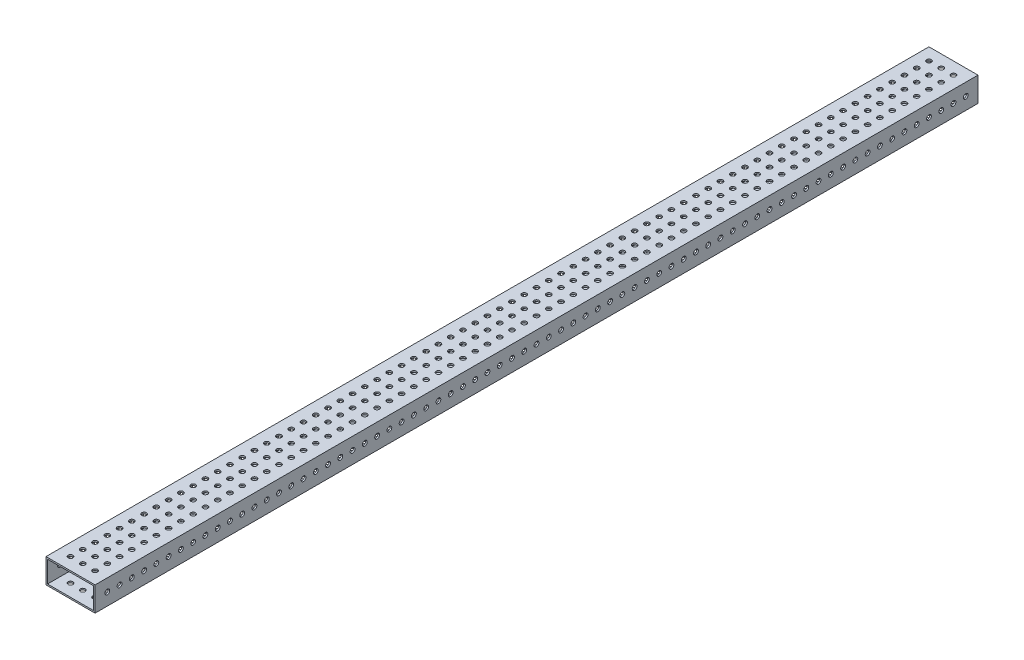
SolidWorks part; units mm, degrees
material "6061 Alloy"
ref_plane "Front Plane" through (0, 0, 0) normal (0, 0, 1) x (1, 0, 0)
ref_plane "Top Plane" through (0, 0, 0) normal (0, 1, 0) x (1, 0, 0)
ref_plane "Right Plane" through (0, 0, 0) normal (1, 0, 0) x (0, 0, -1)
sketch "Sketch1" plane through (0, 0, 0) normal (0, 0, 1) x (1, 0, 0)
  line L0 (1.5875, 1.5875) -> (49.2125, 1.5875)
  line L1 (0, 0) -> (50.8, 0)
  line L2 (0, 0) -> (0, 25.4)
  line L3 (0, 25.4) -> (50.8, 25.4)
  line L4 (50.8, 0) -> (50.8, 25.4)
  line L5 (49.2125, 1.5875) -> (49.2125, 23.8125)
  line L6 (1.5875, 23.8125) -> (49.2125, 23.8125)
  line L7 (1.5875, 1.5875) -> (1.5875, 23.8125)
  dimension "D1" = 50.8
  dimension "D2" = 25.4
  dimension "D3" = 1.5875
extrude "Boss-Extrude1" add sketch "Sketch1" along normal blind 914.4
sketch "Sketch2" plane through (50.8, 0, 0) normal (1, 0, 0) x (0, 0, -1)
  line L0 (-914.4, 0) -> (-914.4, 25.4) construction
  line L1 (-901.7, 12.7) -> (-889, 12.7) construction
  circle A0 centre (-901.7, 12.7) radius 2.4892
  circle A1 centre (-889, 12.7) radius 2.4892
  circle A2 centre (-876.3, 12.7) radius 2.4892
  circle A3 centre (-863.6, 12.7) radius 2.4892
  circle A4 centre (-850.9, 12.7) radius 2.4892
  circle A5 centre (-838.2, 12.7) radius 2.4892
  circle A6 centre (-825.5, 12.7) radius 2.4892
  circle A7 centre (-812.8, 12.7) radius 2.4892
  circle A8 centre (-800.1, 12.7) radius 2.4892
  circle A9 centre (-787.4, 12.7) radius 2.4892
  circle A10 centre (-774.7, 12.7) radius 2.4892
  circle A11 centre (-762, 12.7) radius 2.4892
  circle A12 centre (-749.3, 12.7) radius 2.4892
  circle A13 centre (-736.6, 12.7) radius 2.4892
  circle A14 centre (-723.9, 12.7) radius 2.4892
  circle A15 centre (-711.2, 12.7) radius 2.4892
  circle A16 centre (-698.5, 12.7) radius 2.4892
  circle A17 centre (-685.8, 12.7) radius 2.4892
  circle A18 centre (-673.1, 12.7) radius 2.4892
  circle A19 centre (-660.4, 12.7) radius 2.4892
  circle A20 centre (-647.7, 12.7) radius 2.4892
  circle A21 centre (-635, 12.7) radius 2.4892
  circle A22 centre (-622.3, 12.7) radius 2.4892
  circle A23 centre (-609.6, 12.7) radius 2.4892
  circle A24 centre (-596.9, 12.7) radius 2.4892
  circle A25 centre (-584.2, 12.7) radius 2.4892
  circle A26 centre (-571.5, 12.7) radius 2.4892
  circle A27 centre (-558.8, 12.7) radius 2.4892
  circle A28 centre (-546.1, 12.7) radius 2.4892
  circle A29 centre (-533.4, 12.7) radius 2.4892
  circle A30 centre (-520.7, 12.7) radius 2.4892
  circle A31 centre (-508, 12.7) radius 2.4892
  circle A32 centre (-495.3, 12.7) radius 2.4892
  circle A33 centre (-482.6, 12.7) radius 2.4892
  circle A34 centre (-469.9, 12.7) radius 2.4892
  circle A35 centre (-457.2, 12.7) radius 2.4892
  circle A36 centre (-444.5, 12.7) radius 2.4892
  circle A37 centre (-431.8, 12.7) radius 2.4892
  circle A38 centre (-419.1, 12.7) radius 2.4892
  circle A39 centre (-406.4, 12.7) radius 2.4892
  circle A40 centre (-393.7, 12.7) radius 2.4892
  circle A41 centre (-381, 12.7) radius 2.4892
  circle A42 centre (-368.3, 12.7) radius 2.4892
  circle A43 centre (-355.6, 12.7) radius 2.4892
  circle A44 centre (-342.9, 12.7) radius 2.4892
  circle A45 centre (-330.2, 12.7) radius 2.4892
  circle A46 centre (-317.5, 12.7) radius 2.4892
  circle A47 centre (-304.8, 12.7) radius 2.4892
  circle A48 centre (-292.1, 12.7) radius 2.4892
  circle A49 centre (-279.4, 12.7) radius 2.4892
  circle A50 centre (-266.7, 12.7) radius 2.4892
  circle A51 centre (-254, 12.7) radius 2.4892
  circle A52 centre (-241.3, 12.7) radius 2.4892
  circle A53 centre (-228.6, 12.7) radius 2.4892
  circle A54 centre (-215.9, 12.7) radius 2.4892
  circle A55 centre (-203.2, 12.7) radius 2.4892
  circle A56 centre (-190.5, 12.7) radius 2.4892
  circle A57 centre (-177.8, 12.7) radius 2.4892
  circle A58 centre (-165.1, 12.7) radius 2.4892
  circle A59 centre (-152.4, 12.7) radius 2.4892
  circle A60 centre (-139.7, 12.7) radius 2.4892
  circle A61 centre (-127, 12.7) radius 2.4892
  circle A62 centre (-114.3, 12.7) radius 2.4892
  circle A63 centre (-101.6, 12.7) radius 2.4892
  circle A64 centre (-88.9, 12.7) radius 2.4892
  circle A65 centre (-76.2, 12.7) radius 2.4892
  circle A66 centre (-63.5, 12.7) radius 2.4892
  circle A67 centre (-50.8, 12.7) radius 2.4892
  circle A68 centre (-38.1, 12.7) radius 2.4892
  circle A69 centre (-25.4, 12.7) radius 2.4892
  circle A70 centre (-12.7, 12.7) radius 2.4892
  point P5 (-914.4, 12.7)
  dimension "D1" = 4.9784
  dimension "D3" = 71
  dimension "D2" = 12.7
  dimension "D4" = 12.7
extrude "Cut-Extrude1" cut sketch "Sketch2" against normal through all
sketch "Sketch3" plane through (0, 25.4, 0) normal (0, 1, 0) x (1, 0, 0)
  line L0 (50.8, 0) -> (0, 0) construction
  line L1 (0, -914.4) -> (0, 0) construction
  line L2 (12.7, -12.7) -> (25.4, -12.7) construction
  line L3 (12.7, -12.7) -> (12.7, -25.4) construction
  line L4 (50.8, -914.4) -> (50.8, 0) construction
  circle A0 centre (12.7, -12.7) radius 2.4892
  circle A1 centre (25.4, -12.7) radius 2.4892
  circle A2 centre (38.1, -12.7) radius 2.4892
  circle A3 centre (25.4, -25.4) radius 2.4892
  circle A4 centre (38.1, -25.4) radius 2.4892
  circle A5 centre (25.4, -38.1) radius 2.4892
  circle A6 centre (38.1, -38.1) radius 2.4892
  circle A7 centre (25.4, -50.8) radius 2.4892
  circle A8 centre (38.1, -50.8) radius 2.4892
  circle A9 centre (25.4, -63.5) radius 2.4892
  circle A10 centre (38.1, -63.5) radius 2.4892
  circle A11 centre (25.4, -76.2) radius 2.4892
  circle A12 centre (38.1, -76.2) radius 2.4892
  circle A13 centre (25.4, -88.9) radius 2.4892
  circle A14 centre (38.1, -88.9) radius 2.4892
  circle A15 centre (25.4, -101.6) radius 2.4892
  circle A16 centre (38.1, -101.6) radius 2.4892
  circle A17 centre (25.4, -114.3) radius 2.4892
  circle A18 centre (38.1, -114.3) radius 2.4892
  circle A19 centre (25.4, -127) radius 2.4892
  circle A20 centre (38.1, -127) radius 2.4892
  circle A21 centre (25.4, -139.7) radius 2.4892
  circle A22 centre (38.1, -139.7) radius 2.4892
  circle A23 centre (25.4, -152.4) radius 2.4892
  circle A24 centre (38.1, -152.4) radius 2.4892
  circle A25 centre (25.4, -165.1) radius 2.4892
  circle A26 centre (38.1, -165.1) radius 2.4892
  circle A27 centre (25.4, -177.8) radius 2.4892
  circle A28 centre (38.1, -177.8) radius 2.4892
  circle A29 centre (25.4, -190.5) radius 2.4892
  circle A30 centre (38.1, -190.5) radius 2.4892
  circle A31 centre (25.4, -203.2) radius 2.4892
  circle A32 centre (38.1, -203.2) radius 2.4892
  circle A33 centre (25.4, -215.9) radius 2.4892
  circle A34 centre (38.1, -215.9) radius 2.4892
  circle A35 centre (25.4, -228.6) radius 2.4892
  circle A36 centre (38.1, -228.6) radius 2.4892
  circle A37 centre (25.4, -241.3) radius 2.4892
  circle A38 centre (38.1, -241.3) radius 2.4892
  circle A39 centre (25.4, -254) radius 2.4892
  circle A40 centre (38.1, -254) radius 2.4892
  circle A41 centre (25.4, -266.7) radius 2.4892
  circle A42 centre (38.1, -266.7) radius 2.4892
  circle A43 centre (25.4, -279.4) radius 2.4892
  circle A44 centre (38.1, -279.4) radius 2.4892
  circle A45 centre (25.4, -292.1) radius 2.4892
  circle A46 centre (38.1, -292.1) radius 2.4892
  circle A47 centre (25.4, -304.8) radius 2.4892
  circle A48 centre (38.1, -304.8) radius 2.4892
  circle A49 centre (25.4, -317.5) radius 2.4892
  circle A50 centre (38.1, -317.5) radius 2.4892
  circle A51 centre (25.4, -330.2) radius 2.4892
  circle A52 centre (38.1, -330.2) radius 2.4892
  circle A53 centre (25.4, -342.9) radius 2.4892
  circle A54 centre (38.1, -342.9) radius 2.4892
  circle A55 centre (25.4, -355.6) radius 2.4892
  circle A56 centre (38.1, -355.6) radius 2.4892
  circle A57 centre (25.4, -368.3) radius 2.4892
  circle A58 centre (38.1, -368.3) radius 2.4892
  circle A59 centre (25.4, -381) radius 2.4892
  circle A60 centre (38.1, -381) radius 2.4892
  circle A61 centre (25.4, -393.7) radius 2.4892
  circle A62 centre (38.1, -393.7) radius 2.4892
  circle A63 centre (25.4, -406.4) radius 2.4892
  circle A64 centre (38.1, -406.4) radius 2.4892
  circle A65 centre (25.4, -419.1) radius 2.4892
  circle A66 centre (38.1, -419.1) radius 2.4892
  circle A67 centre (25.4, -431.8) radius 2.4892
  circle A68 centre (38.1, -431.8) radius 2.4892
  circle A69 centre (25.4, -444.5) radius 2.4892
  circle A70 centre (38.1, -444.5) radius 2.4892
  circle A71 centre (25.4, -457.2) radius 2.4892
  circle A72 centre (38.1, -457.2) radius 2.4892
  circle A73 centre (25.4, -469.9) radius 2.4892
  circle A74 centre (38.1, -469.9) radius 2.4892
  circle A75 centre (25.4, -482.6) radius 2.4892
  circle A76 centre (38.1, -482.6) radius 2.4892
  circle A77 centre (25.4, -495.3) radius 2.4892
  circle A78 centre (38.1, -495.3) radius 2.4892
  circle A79 centre (25.4, -508) radius 2.4892
  circle A80 centre (38.1, -508) radius 2.4892
  circle A81 centre (25.4, -520.7) radius 2.4892
  circle A82 centre (38.1, -520.7) radius 2.4892
  circle A83 centre (25.4, -533.4) radius 2.4892
  circle A84 centre (38.1, -533.4) radius 2.4892
  circle A85 centre (25.4, -546.1) radius 2.4892
  circle A86 centre (38.1, -546.1) radius 2.4892
  circle A87 centre (25.4, -558.8) radius 2.4892
  circle A88 centre (38.1, -558.8) radius 2.4892
  circle A89 centre (25.4, -571.5) radius 2.4892
  circle A90 centre (38.1, -571.5) radius 2.4892
  circle A91 centre (25.4, -584.2) radius 2.4892
  circle A92 centre (38.1, -584.2) radius 2.4892
  circle A93 centre (25.4, -596.9) radius 2.4892
  circle A94 centre (38.1, -596.9) radius 2.4892
  circle A95 centre (25.4, -609.6) radius 2.4892
  circle A96 centre (38.1, -609.6) radius 2.4892
  circle A97 centre (25.4, -622.3) radius 2.4892
  circle A98 centre (38.1, -622.3) radius 2.4892
  circle A99 centre (25.4, -635) radius 2.4892
  circle A100 centre (38.1, -635) radius 2.4892
  circle A101 centre (25.4, -647.7) radius 2.4892
  circle A102 centre (38.1, -647.7) radius 2.4892
  circle A103 centre (25.4, -660.4) radius 2.4892
  circle A104 centre (38.1, -660.4) radius 2.4892
  circle A105 centre (25.4, -673.1) radius 2.4892
  circle A106 centre (38.1, -673.1) radius 2.4892
  circle A107 centre (25.4, -685.8) radius 2.4892
  circle A108 centre (38.1, -685.8) radius 2.4892
  circle A109 centre (25.4, -698.5) radius 2.4892
  circle A110 centre (38.1, -698.5) radius 2.4892
  circle A111 centre (25.4, -711.2) radius 2.4892
  circle A112 centre (38.1, -711.2) radius 2.4892
  circle A113 centre (25.4, -723.9) radius 2.4892
  circle A114 centre (38.1, -723.9) radius 2.4892
  circle A115 centre (25.4, -736.6) radius 2.4892
  circle A116 centre (38.1, -736.6) radius 2.4892
  circle A117 centre (25.4, -749.3) radius 2.4892
  circle A118 centre (38.1, -749.3) radius 2.4892
  circle A119 centre (25.4, -762) radius 2.4892
  circle A120 centre (38.1, -762) radius 2.4892
  circle A121 centre (25.4, -774.7) radius 2.4892
  circle A122 centre (38.1, -774.7) radius 2.4892
  circle A123 centre (25.4, -787.4) radius 2.4892
  circle A124 centre (38.1, -787.4) radius 2.4892
  circle A125 centre (25.4, -800.1) radius 2.4892
  circle A126 centre (38.1, -800.1) radius 2.4892
  circle A127 centre (25.4, -812.8) radius 2.4892
  circle A128 centre (38.1, -812.8) radius 2.4892
  circle A129 centre (25.4, -825.5) radius 2.4892
  circle A130 centre (38.1, -825.5) radius 2.4892
  circle A131 centre (25.4, -838.2) radius 2.4892
  circle A132 centre (38.1, -838.2) radius 2.4892
  circle A133 centre (25.4, -850.9) radius 2.4892
  circle A134 centre (38.1, -850.9) radius 2.4892
  circle A135 centre (25.4, -863.6) radius 2.4892
  circle A136 centre (38.1, -863.6) radius 2.4892
  circle A137 centre (25.4, -876.3) radius 2.4892
  circle A138 centre (38.1, -876.3) radius 2.4892
  circle A139 centre (25.4, -889) radius 2.4892
  circle A140 centre (38.1, -889) radius 2.4892
  circle A141 centre (25.4, -901.7) radius 2.4892
  circle A142 centre (38.1, -901.7) radius 2.4892
  circle A145 centre (12.7, -25.4) radius 2.4892
  circle A146 centre (12.7, -38.1) radius 2.4892
  circle A147 centre (12.7, -50.8) radius 2.4892
  circle A148 centre (12.7, -63.5) radius 2.4892
  circle A149 centre (12.7, -76.2) radius 2.4892
  circle A150 centre (12.7, -88.9) radius 2.4892
  circle A151 centre (12.7, -101.6) radius 2.4892
  circle A152 centre (12.7, -114.3) radius 2.4892
  circle A153 centre (12.7, -127) radius 2.4892
  circle A154 centre (12.7, -139.7) radius 2.4892
  circle A155 centre (12.7, -152.4) radius 2.4892
  circle A156 centre (12.7, -165.1) radius 2.4892
  circle A157 centre (12.7, -177.8) radius 2.4892
  circle A158 centre (12.7, -190.5) radius 2.4892
  circle A159 centre (12.7, -203.2) radius 2.4892
  circle A160 centre (12.7, -215.9) radius 2.4892
  circle A161 centre (12.7, -228.6) radius 2.4892
  circle A162 centre (12.7, -241.3) radius 2.4892
  circle A163 centre (12.7, -254) radius 2.4892
  circle A164 centre (12.7, -266.7) radius 2.4892
  circle A165 centre (12.7, -279.4) radius 2.4892
  circle A166 centre (12.7, -292.1) radius 2.4892
  circle A167 centre (12.7, -304.8) radius 2.4892
  circle A168 centre (12.7, -317.5) radius 2.4892
  circle A169 centre (12.7, -330.2) radius 2.4892
  circle A170 centre (12.7, -342.9) radius 2.4892
  circle A171 centre (12.7, -355.6) radius 2.4892
  circle A172 centre (12.7, -368.3) radius 2.4892
  circle A173 centre (12.7, -381) radius 2.4892
  circle A174 centre (12.7, -393.7) radius 2.4892
  circle A175 centre (12.7, -406.4) radius 2.4892
  circle A176 centre (12.7, -419.1) radius 2.4892
  circle A177 centre (12.7, -431.8) radius 2.4892
  circle A178 centre (12.7, -444.5) radius 2.4892
  circle A179 centre (12.7, -457.2) radius 2.4892
  circle A180 centre (12.7, -469.9) radius 2.4892
  circle A181 centre (12.7, -482.6) radius 2.4892
  circle A182 centre (12.7, -495.3) radius 2.4892
  circle A183 centre (12.7, -508) radius 2.4892
  circle A184 centre (12.7, -520.7) radius 2.4892
  circle A185 centre (12.7, -533.4) radius 2.4892
  circle A186 centre (12.7, -546.1) radius 2.4892
  circle A187 centre (12.7, -558.8) radius 2.4892
  circle A188 centre (12.7, -571.5) radius 2.4892
  circle A189 centre (12.7, -584.2) radius 2.4892
  circle A190 centre (12.7, -596.9) radius 2.4892
  circle A191 centre (12.7, -609.6) radius 2.4892
  circle A192 centre (12.7, -622.3) radius 2.4892
  circle A193 centre (12.7, -635) radius 2.4892
  circle A194 centre (12.7, -647.7) radius 2.4892
  circle A195 centre (12.7, -660.4) radius 2.4892
  circle A196 centre (12.7, -673.1) radius 2.4892
  circle A197 centre (12.7, -685.8) radius 2.4892
  circle A198 centre (12.7, -698.5) radius 2.4892
  circle A199 centre (12.7, -711.2) radius 2.4892
  circle A200 centre (12.7, -723.9) radius 2.4892
  circle A201 centre (12.7, -736.6) radius 2.4892
  circle A202 centre (12.7, -749.3) radius 2.4892
  circle A203 centre (12.7, -762) radius 2.4892
  circle A204 centre (12.7, -774.7) radius 2.4892
  circle A205 centre (12.7, -787.4) radius 2.4892
  circle A206 centre (12.7, -800.1) radius 2.4892
  circle A207 centre (12.7, -812.8) radius 2.4892
  circle A208 centre (12.7, -825.5) radius 2.4892
  circle A209 centre (12.7, -838.2) radius 2.4892
  circle A210 centre (12.7, -850.9) radius 2.4892
  circle A211 centre (12.7, -863.6) radius 2.4892
  circle A212 centre (12.7, -876.3) radius 2.4892
  circle A213 centre (12.7, -889) radius 2.4892
  circle A214 centre (12.7, -901.7) radius 2.4892
  dimension "D1" = 4.9784
  dimension "D2" = 12.7
  dimension "D3" = 12.7
  dimension "D6" = 12.7
  dimension "D7" = 12.7
  dimension "D8" = 12.7
  dimension "D4" = 3
  dimension "D5" = 71
extrude "Cut-Extrude2" cut sketch "Sketch3" against normal through all
